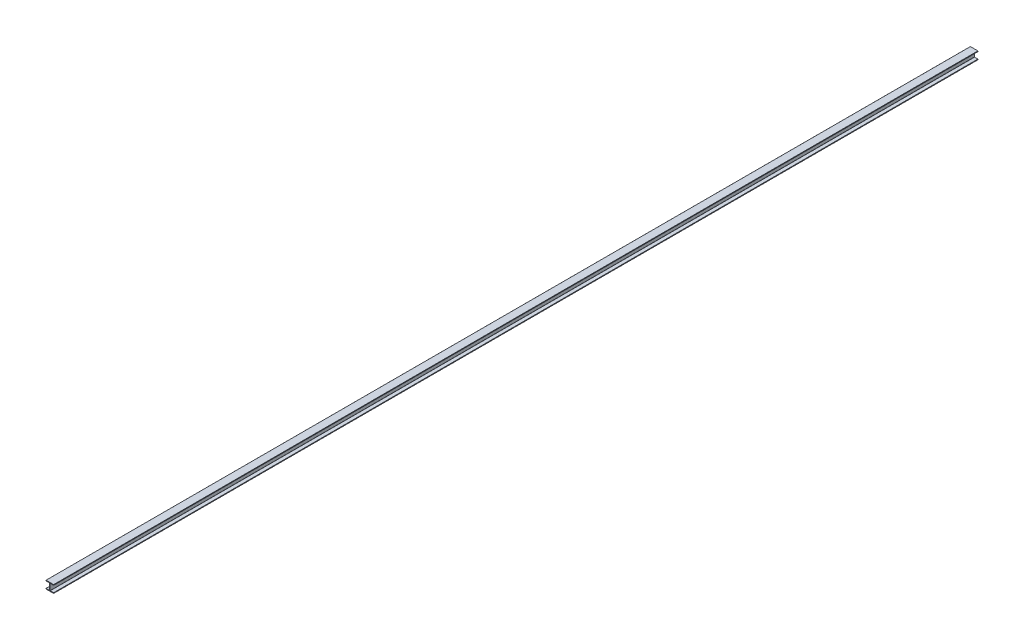
SolidWorks part; units mm, degrees
ref_plane "Front Plane" through (0, 0, 0) normal (0, 0, 1) x (1, 0, 0)
ref_plane "Top Plane" through (0, 0, 0) normal (0, 1, 0) x (1, 0, 0)
ref_plane "Right Plane" through (0, 0, 0) normal (1, 0, 0) x (0, 0, -1)
sketch "Rail Cross Section" plane through (0, 0, 0) normal (0, 0, 1) x (1, 0, 0)
  line L1 (-63.5, -61.976) -> (-63.5, -54.5592)
  line L2 (-61.976, -53.0352) -> (-6.7691, -53.0352)
  line L3 (-5.2451, -51.5112) -> (-5.2451, 51.5112)
  line L4 (-6.7691, 53.0352) -> (-61.976, 53.0352)
  line L5 (-63.5, 54.5592) -> (-63.5, 61.976)
  line L6 (-61.976, 63.5) -> (61.976, 63.5)
  line L7 (63.5, 61.976) -> (63.5, 54.5592)
  line L10 (61.976, 53.0352) -> (6.7691, 53.0352)
  line L11 (5.2451, 51.5112) -> (5.2451, -51.5112)
  line L12 (6.7691, -53.0352) -> (61.976, -53.0352)
  line L13 (63.5, -54.5592) -> (63.5, -61.976)
  line L15 (61.976, -63.5) -> (-61.976, -63.5)
  line L16 (0, 63.5) -> (0, -63.5) construction
  line L17 (-5.2451, 0) -> (5.2451, 0) construction
  arc A0 (-63.5, -61.976) -> (-61.976, -63.5) centre (-61.976, -61.976) ccw
  arc A1 (-63.5, -54.5592) -> (-61.976, -53.0352) centre (-61.976, -54.5592) cw
  arc A2 (63.5, -61.976) -> (61.976, -63.5) centre (61.976, -61.976) cw
  arc A3 (61.976, -53.0352) -> (63.5, -54.5592) centre (61.976, -54.5592) cw
  arc A4 (5.2451, -51.5112) -> (6.7691, -53.0352) centre (6.7691, -51.5112) ccw
  arc A5 (-6.7691, -53.0352) -> (-5.2451, -51.5112) centre (-6.7691, -51.5112) ccw
  arc A6 (63.5, 54.5592) -> (61.976, 53.0352) centre (61.976, 54.5592) cw
  arc A7 (61.976, 63.5) -> (63.5, 61.976) centre (61.976, 61.976) cw
  arc A8 (6.7691, 53.0352) -> (5.2451, 51.5112) centre (6.7691, 51.5112) ccw
  arc A9 (-5.2451, 51.5112) -> (-6.7691, 53.0352) centre (-6.7691, 51.5112) ccw
  arc A10 (-61.976, 53.0352) -> (-63.5, 54.5592) centre (-61.976, 54.5592) cw
  arc A11 (-63.5, 61.976) -> (-61.976, 63.5) centre (-61.976, 61.976) cw
  point P7 (0, 0)
  point P19 (-63.5, -63.5)
  point P28 (63.5, -63.5)
  point P37 (63.5, 53.0352)
  point P40 (63.5, 63.5)
  dimension "D5" = 1.524
  dimension "D1" = 10.4648
  dimension "D2" = 10.4902
  dimension "D3" = 127
  dimension "D4" = 127
extrude "Rail" add sketch "Rail Cross Section" along normal mid plane 15240
